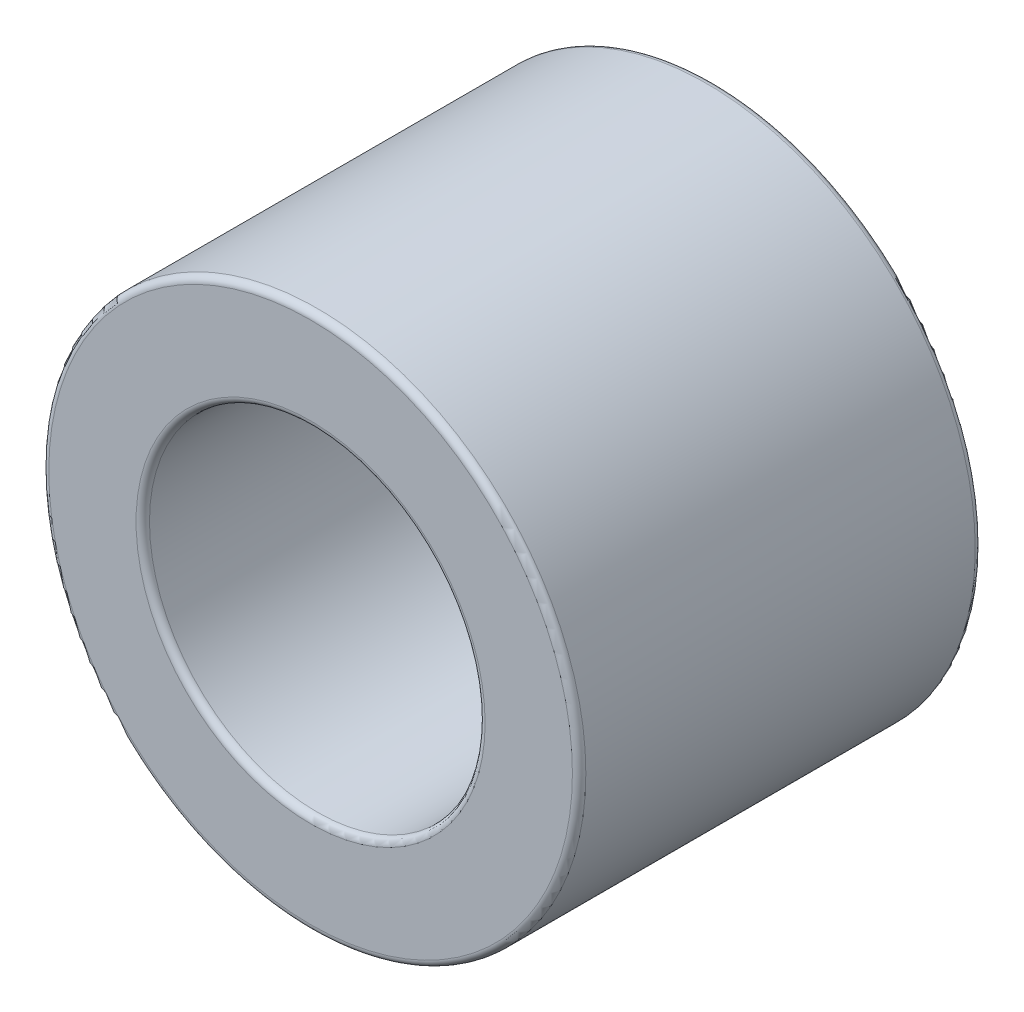
SolidWorks part; units mm, degrees
ref_plane "Front" through (0, 0, 0) normal (0, 0, 1) x (1, 0, 0)
ref_plane "Top" through (0, 0, 0) normal (0, 1, 0) x (1, 0, 0)
ref_plane "Right" through (0, 0, 0) normal (1, 0, 0) x (0, 0, -1)
sketch "Sketch1" plane through (0, 0, 0) normal (0, 0, 1) x (1, 0, 0)
  circle A0 centre (0, 0) radius 2.5
  circle A1 centre (0, 0) radius 4
  dimension "D1" = 8
  dimension "D2" = 5
extrude "Boss-Extrude1" add sketch "Sketch1" along normal blind 6
fillet "Fillet1" radius 0.1 4 edges at (2.5, 0, 0) (4, 0, 0) (2.5, 0, 6) (4, 0, 6)
